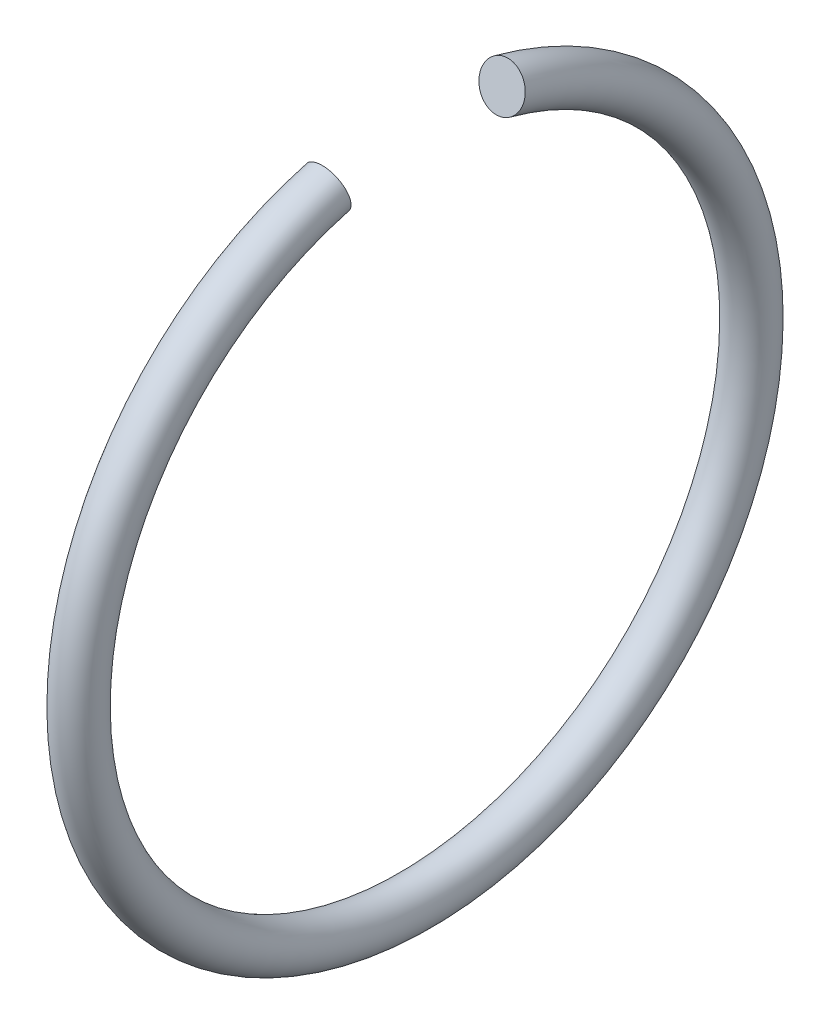
SolidWorks part; units mm, degrees
material "3.1645 (EN-AW 2030)"
ref_plane "Přední rovina" through (0, 0, 0) normal (0, 0, 1) x (1, 0, 0)
ref_plane "Horní rovina" through (0, 0, 0) normal (0, 1, 0) x (1, 0, 0)
ref_plane "Pravá rovina" through (0, 0, 0) normal (1, 0, 0) x (0, 0, -1)
sketch "Skica1" plane through (0, 0, 0) normal (0, 0, 1) x (1, 0, 0)
  line L0 (-67.4823, 0) -> (-363.0393, 0) construction
  line L1 (-67.4823, 0) -> (-363.0393, 0) construction
  circle A0 centre (-325.05, -15) radius 1 construction
  circle A1 centre (-325.05, -15) radius 1
revolve "Rotovat1" add sketch "Skica1" angle 330 mid plane about L1
